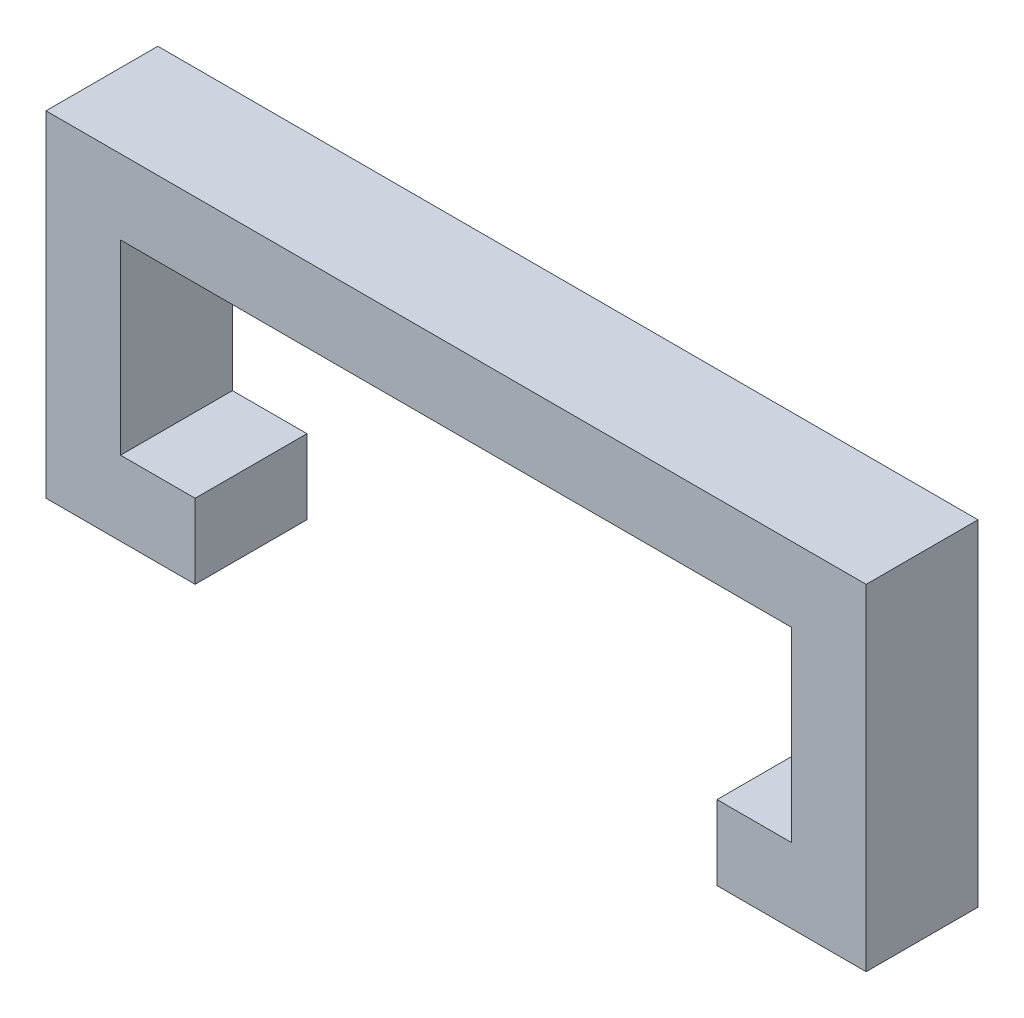
SolidWorks part; units mm, degrees
ref_plane "Front Plane" through (0, 0, 0) normal (0, 0, 1) x (1, 0, 0)
ref_plane "Top Plane" through (0, 0, 0) normal (0, 1, 0) x (1, 0, 0)
ref_plane "Right Plane" through (0, 0, 0) normal (1, 0, 0) x (0, 0, -1)
sketch "Sketch1" plane through (0, 0, 0) normal (0, 0, 1) x (1, 0, 0)
  line L0 (12.9337, -5.3787) -> (12.9337, -10.4587)
  line L1 (-32.7863, 12.4013) -> (23.0937, 12.4013)
  line L2 (-32.7863, 12.4013) -> (-32.7863, -10.4587)
  line L3 (-32.7863, -10.4587) -> (-22.6263, -10.4587)
  line L4 (23.0937, 12.4013) -> (23.0937, -10.4587)
  line L5 (-27.7063, 7.3213) -> (18.0137, 7.3213)
  line L6 (-27.7063, 7.3213) -> (-27.7063, -5.3787)
  line L7 (-27.7063, -5.3787) -> (-22.6263, -5.3787)
  line L8 (18.0137, 7.3213) -> (18.0137, -5.3787)
  line L9 (-22.6263, -5.3787) -> (-22.6263, -10.4587)
  line L10 (12.9337, -10.4587) -> (23.0937, -10.4587)
  line L11 (12.9337, -5.3787) -> (18.0137, -5.3787)
  dimension "D1" = 55.88
  dimension "D2" = 22.86
  dimension "D3" = 5.08
  dimension "D4" = 5.08
  dimension "D5" = 5.08
  dimension "D6" = 5.08
  dimension "D7" = 10.16
extrude "Boss-Extrude1" add sketch "Sketch1" along normal blind 7.62
